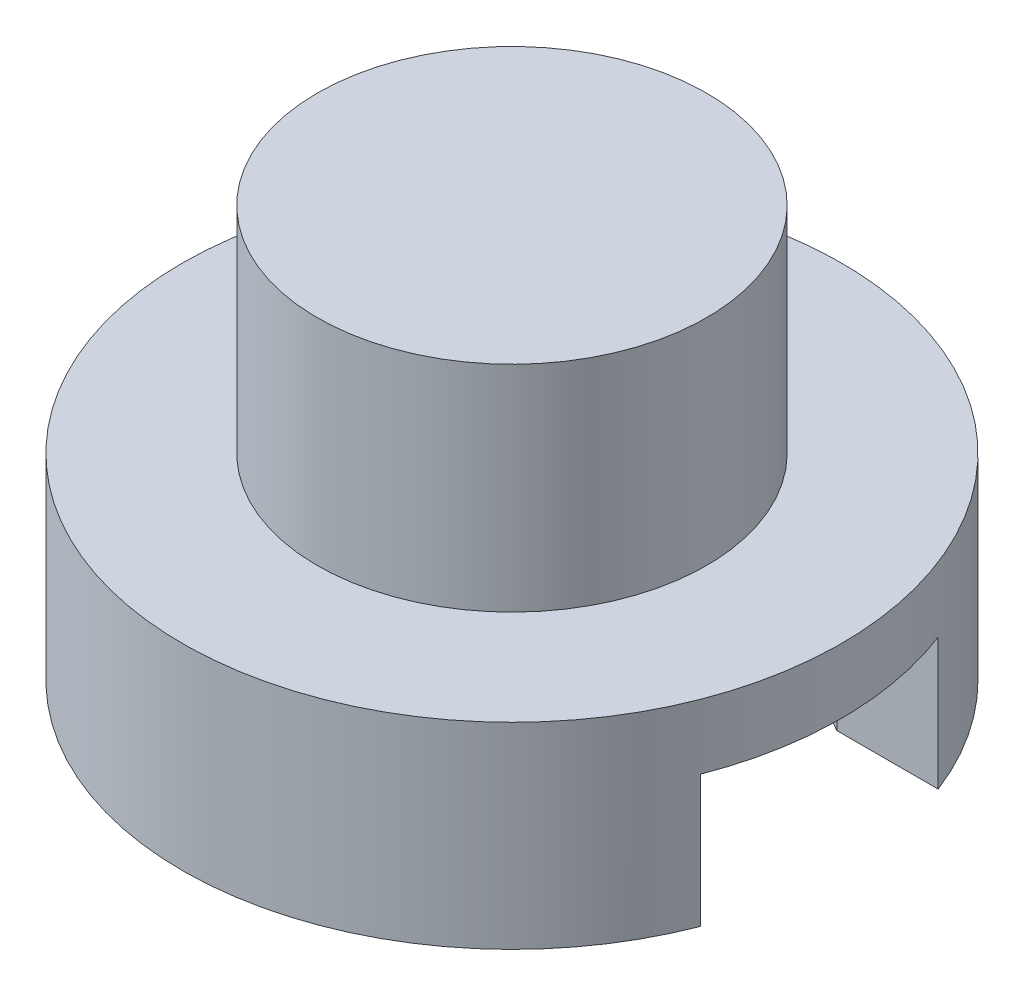
SolidWorks part; units mm, degrees
ref_plane "Front Plane" through (0, 0, 0) normal (0, 0, 1) x (1, 0, 0)
ref_plane "Top Plane" through (0, 0, 0) normal (0, 1, 0) x (1, 0, 0)
ref_plane "Right Plane" through (0, 0, 0) normal (1, 0, 0) x (0, 0, -1)
sketch "Sketch1" plane through (0, 0, 0) normal (0, 0, 1) x (1, 0, 0)
  line L0 (-10.1895, 0) -> (-10.1895, 9)
  line L1 (-10.1895, 9) -> (15.2105, 9)
  line L2 (15.2105, 9) -> (15.2105, 0)
  line L3 (15.2105, 0) -> (21.2105, 0)
  line L4 (21.2105, 0) -> (21.2105, 20.1735)
  line L5 (21.2105, 20.1735) -> (-16.1895, 20.1735)
  line L6 (-16.1895, 20.1735) -> (-16.1895, 0)
  line L7 (-16.1895, 0) -> (-10.1895, 0)
  dimension "D1" = 25.4
  dimension "D2" = 9
  dimension "D3" = 20.1735
  dimension "D4" = 6
  dimension "D5" = 6
extrude "Boss-Extrude1" add sketch "Sketch1" along normal blind 25.4
sketch "Sketch3" plane through (0, 20.1735, 0) normal (0, 1, 0) x (1, 0, 0)
  line L0 (21.2105, -12.7) -> (-16.1895, -12.7) construction
  line L1 (21.2105, -25.4) -> (21.2105, 0) construction
  line L13 (-16.1895, -25.4) -> (-16.1895, 0) construction
  line L14 (21.2105, 0) -> (-16.1895, 0) construction
  line L15 (-16.1895, -12.7) -> (21.2105, -12.7) construction
  line L17 (10.448, -17.2827) -> (10.448, -8.1173)
  line L18 (10.448, -8.1173) -> (2.5105, -3.5346)
  line L19 (2.5105, -3.5346) -> (-5.427, -8.1173)
  line L20 (-5.427, -8.1173) -> (-5.427, -17.2827)
  line L21 (-5.427, -17.2827) -> (2.5105, -21.8654)
  line L22 (2.5105, -21.8654) -> (10.448, -17.2827)
  line L23 (21.2105, -8.1173) -> (10.448, -8.1173)
  line L24 (21.2105, -8.1173) -> (21.2105, -17.2827)
  line L25 (21.2105, -17.2827) -> (10.448, -17.2827)
  line L26 (10.448, -8.1173) -> (10.448, -17.2827)
  circle A2 centre (2.5105, -12.7) radius 7.9375 construction
  circle A3 centre (2.5105, -12.7) radius 12.7
  dimension "D1" = 15.875
extrude "Boss-Extrude3" add sketch "Sketch3" along normal blind 5.08 contours A3 L25 L22 L21 L20 L19 L18 L23
sketch "Sketch4" plane through (0, 20.1735, 0) normal (0, 1, 0) x (1, 0, 0)
  line L1 (21.2105, 0) -> (-16.1895, 0)
  line L2 (21.2105, 0) -> (21.2105, -25.4)
  line L3 (21.2105, -25.4) -> (-16.1895, -25.4)
  line L4 (-16.1895, 0) -> (-16.1895, -25.4)
extrude "Cut-Extrude1" cut sketch "Sketch4" against normal blind 25.4
sketch "Sketch5" plane through (0, 25.2535, 0) normal (0, 1, 0) x (1, 0, 0)
  line L7 (14.3548, -17.2827) -> (10.448, -17.2827)
  line L8 (10.448, -17.2827) -> (2.5105, -21.8654)
  line L9 (2.5105, -21.8654) -> (-5.427, -17.2827)
  line L10 (-5.427, -17.2827) -> (-5.427, -8.1173)
  line L11 (-5.427, -8.1173) -> (2.5105, -3.5346)
  line L12 (2.5105, -3.5346) -> (10.448, -8.1173)
  line L13 (10.448, -8.1173) -> (14.3548, -8.1173)
  line L14 (14.3548, -17.2827) -> (10.448, -17.2827)
  line L15 (10.448, -17.2827) -> (2.5105, -21.8654)
  line L16 (2.5105, -21.8654) -> (-5.427, -17.2827)
  line L17 (-5.427, -17.2827) -> (-5.427, -8.1173)
  line L18 (-5.427, -8.1173) -> (2.5105, -3.5346)
  line L19 (2.5105, -3.5346) -> (10.448, -8.1173)
  line L20 (10.448, -8.1173) -> (14.3548, -8.1173)
  circle A1 centre (2.5105, -12.7) radius 12.7
  arc A2 (14.3548, -8.1173) -> (14.3548, -17.2827) centre (2.5105, -12.7) ccw
  arc A3 (14.3548, -8.1173) -> (14.3548, -17.2827) centre (2.5105, -12.7) ccw
  dimension "D1" = 0
extrude "Boss-Extrude4" add sketch "Sketch5" along normal blind 2.5 contours A1
sketch "Sketch6" plane through (0, 27.7535, 0) normal (0, 1, 0) x (1, 0, 0)
  circle A1 centre (2.5105, -12.7) radius 7.5
  circle A2 centre (2.5105, -12.7) radius 12.7
  circle A3 centre (2.5105, -12.7) radius 12.7
  dimension "D1" = 0
  dimension "D2" = 15
extrude "Boss-Extrude5" add sketch "Sketch6" along normal blind 8.272 contours A1
